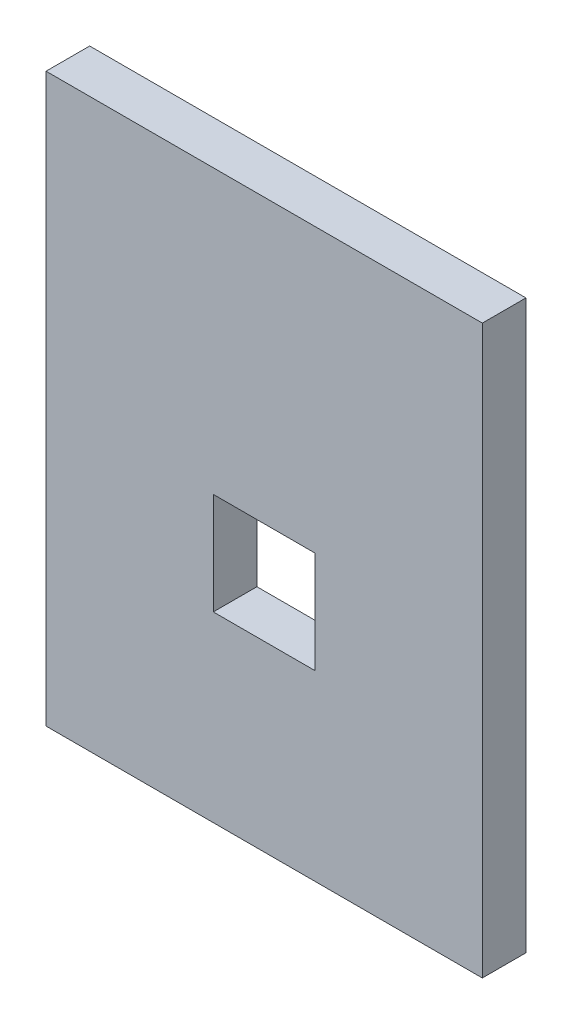
SolidWorks part; units mm, degrees
ref_plane "Front Plane" through (0, 0, 0) normal (0, 0, 1) x (1, 0, 0)
ref_plane "Top Plane" through (0, 0, 0) normal (0, 1, 0) x (1, 0, 0)
ref_plane "Right Plane" through (0, 0, 0) normal (1, 0, 0) x (0, 0, -1)
sketch "Sketch2" plane through (0, 0, 0) normal (0, 0, 1) x (1, 0, 0)
  line L1 (-95.25, -123.825) -> (95.25, -123.825)
  line L2 (-95.25, -123.825) -> (-95.25, 123.825)
  line L3 (-95.25, 123.825) -> (95.25, 123.825)
  line L4 (95.25, -123.825) -> (95.25, 123.825)
  line L5 (-95.25, -123.825) -> (95.25, 123.825) construction
  line L6 (-95.25, 123.825) -> (95.25, -123.825) construction
  line L7 (-22.225, -44.1325) -> (22.225, -44.1325)
  line L8 (-22.225, -44.1325) -> (-22.225, 0.3175)
  line L9 (-22.225, 0.3175) -> (22.225, 0.3175)
  line L10 (22.225, -44.1325) -> (22.225, 0.3175)
  line L11 (-22.225, -44.1325) -> (22.225, 0.3175) construction
  line L12 (-22.225, 0.3175) -> (22.225, -44.1325) construction
  point P0 (0, 0)
  point P6 (0, -21.9075)
  dimension "D1" = 190.5
  dimension "D2" = 247.65
  dimension "D3" = 44.45
  dimension "D4" = 79.6925
extrude "Boss-Extrude1" add sketch "Sketch2" along normal blind 19.05
